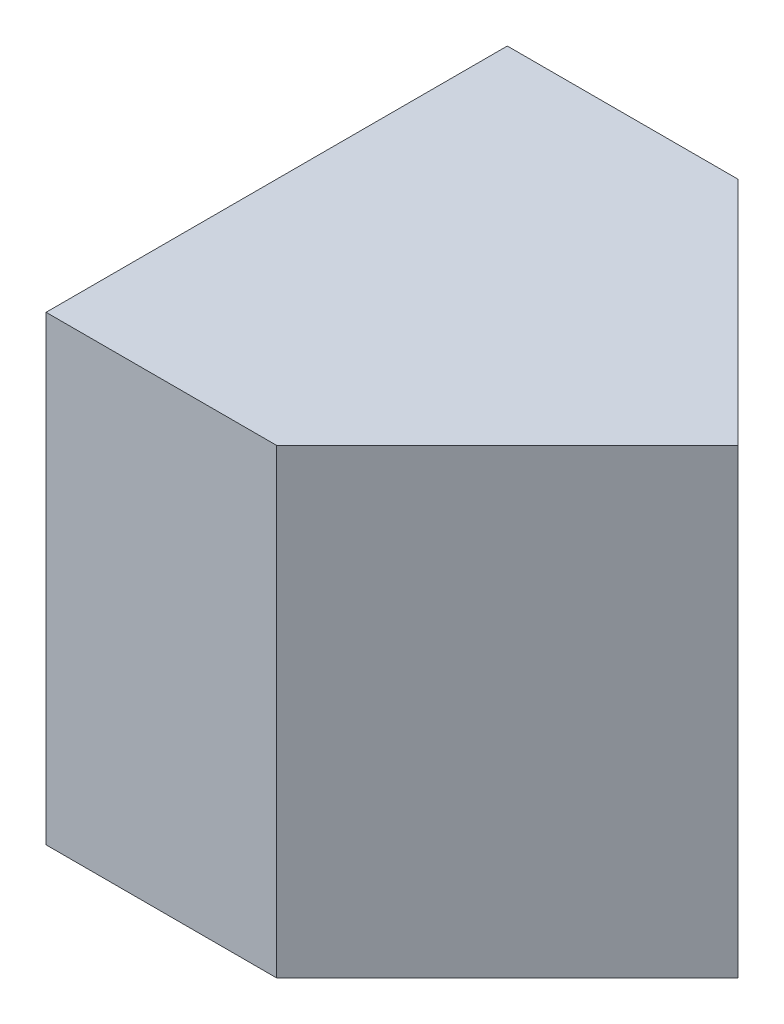
SolidWorks part; units mm, degrees
ref_plane "Front Plane" through (0, 0, 0) normal (0, 0, 1) x (1, 0, 0)
ref_plane "Top Plane" through (0, 0, 0) normal (0, 1, 0) x (1, 0, 0)
ref_plane "Right Plane" through (0, 0, 0) normal (1, 0, 0) x (0, 0, -1)
sketch "Sketch1" plane through (0, 0, 0) normal (0, 0, 1) x (1, 0, 0)
  line L1 (0, 0) -> (20, 0)
  line L2 (0, 0) -> (0, 20)
  line L3 (0, 20) -> (20, 20)
  line L4 (20, 0) -> (20, 20)
  dimension "D1" = 20
  dimension "D2" = 20
extrude "Boss-Extrude1" add sketch "Sketch1" along normal blind 20
sketch "Sketch2" plane through (0, 20, 0) normal (0, 1, 0) x (1, 0, 0)
  line L0 (20, 0) -> (10, 0)
  line L1 (20, 0) -> (0, 0) construction
  line L2 (10, 0) -> (20, -10)
  line L3 (20, -20) -> (20, 0) construction
  line L4 (20, -10) -> (20, 0)
extrude "Cut-Extrude1" cut sketch "Sketch2" against normal blind 20
sketch "Sketch3" plane through (0, 20, 0) normal (0, 1, 0) x (1, 0, 0)
  line L0 (20, -20) -> (10, -20)
  line L1 (20, -20) -> (0, -20) construction
  line L2 (10, -20) -> (20, -10)
  line L3 (20, -10) -> (20, -20)
extrude "Cut-Extrude2" cut sketch "Sketch3" against normal blind 20
